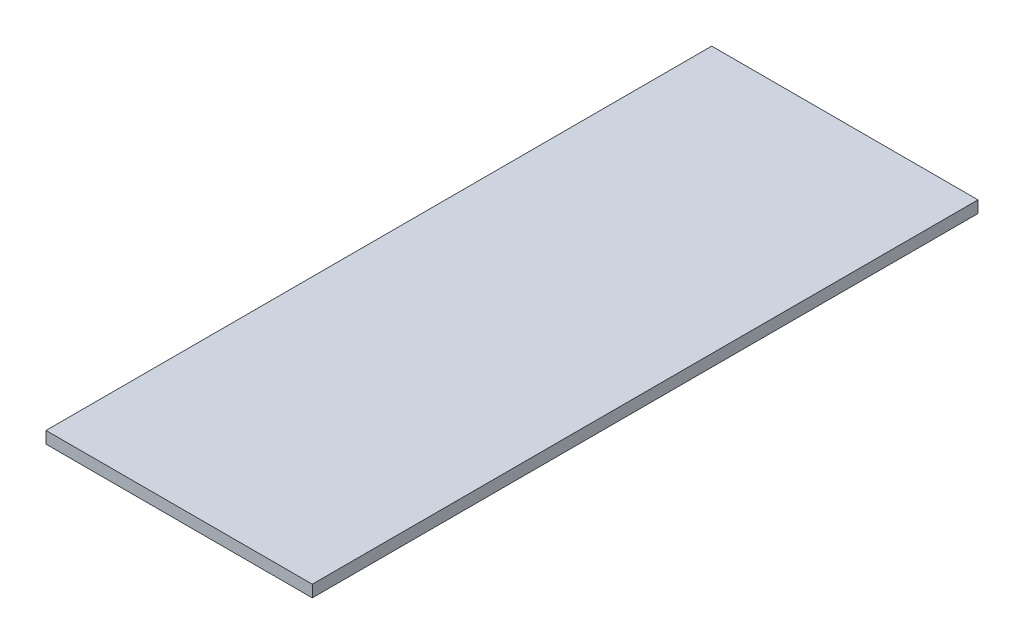
SolidWorks part; units mm, degrees
ref_plane "Front Plane" through (0, 0, 0) normal (0, 0, 1) x (1, 0, 0)
ref_plane "Top Plane" through (0, 0, 0) normal (0, 1, 0) x (1, 0, 0)
ref_plane "Right Plane" through (0, 0, 0) normal (1, 0, 0) x (0, 0, -1)
sketch "Sketch1" plane through (0, 0, 0) normal (0, 1, 0) x (1, 0, 0)
  line L1 (0, 0) -> (71.12, 0)
  line L2 (0, 0) -> (0, 177.8)
  line L3 (0, 177.8) -> (71.12, 177.8)
  line L4 (71.12, 0) -> (71.12, 177.8)
  dimension "D1" = 71.12
  dimension "D2" = 177.8
extrude "Boss-Extrude1" add sketch "Sketch1" along normal blind 3.175
